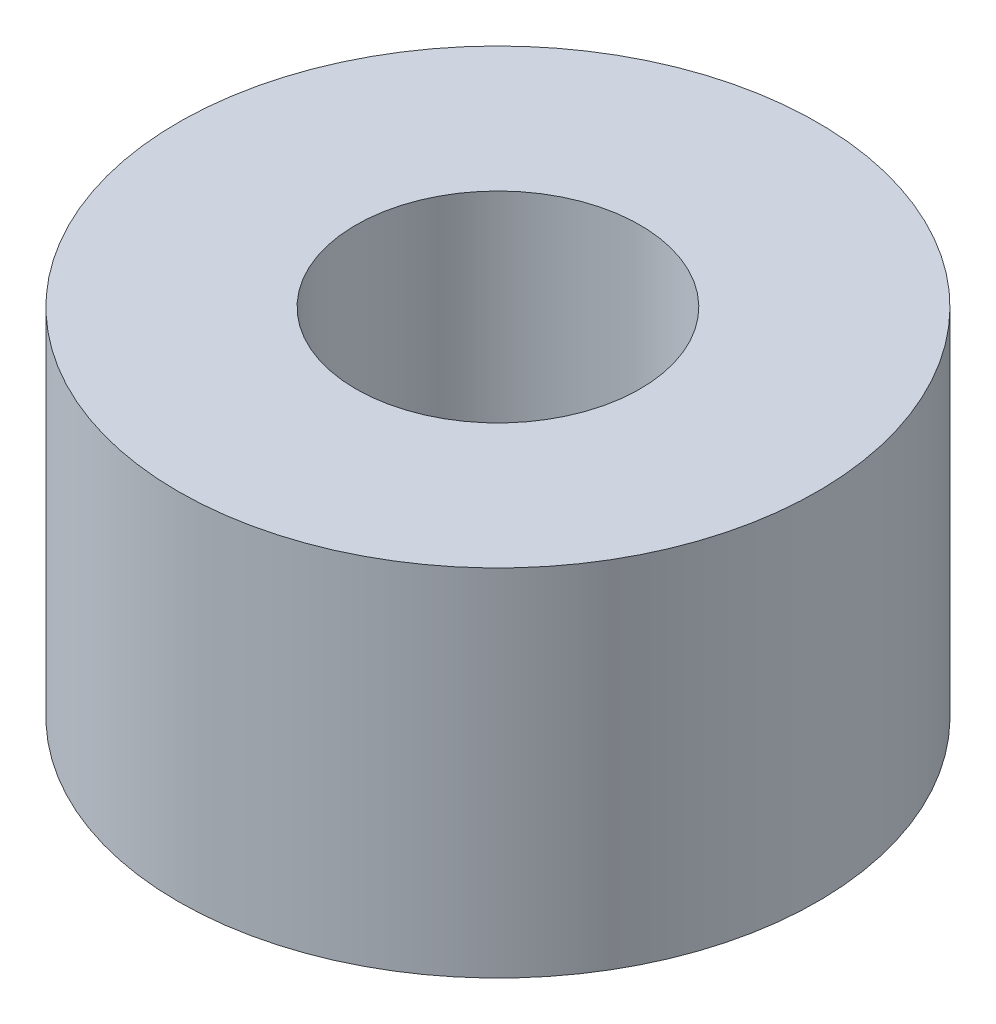
SolidWorks part; units mm, degrees
ref_plane "Front Plane" through (0, 0, 0) normal (0, 0, 1) x (1, 0, 0)
ref_plane "Top Plane" through (0, 0, 0) normal (0, 1, 0) x (1, 0, 0)
ref_plane "Right Plane" through (0, 0, 0) normal (1, 0, 0) x (0, 0, -1)
sketch "Sketch1" plane through (0, 0, 0) normal (0, 1, 0) x (1, 0, 0)
  circle A0 centre (0, 0) radius 1
  circle A1 centre (0, 0) radius 2.25
  dimension "D1" = 2
  dimension "D2" = 4.5
extrude "Boss-Extrude1" add sketch "Sketch1" along normal blind 2.5
